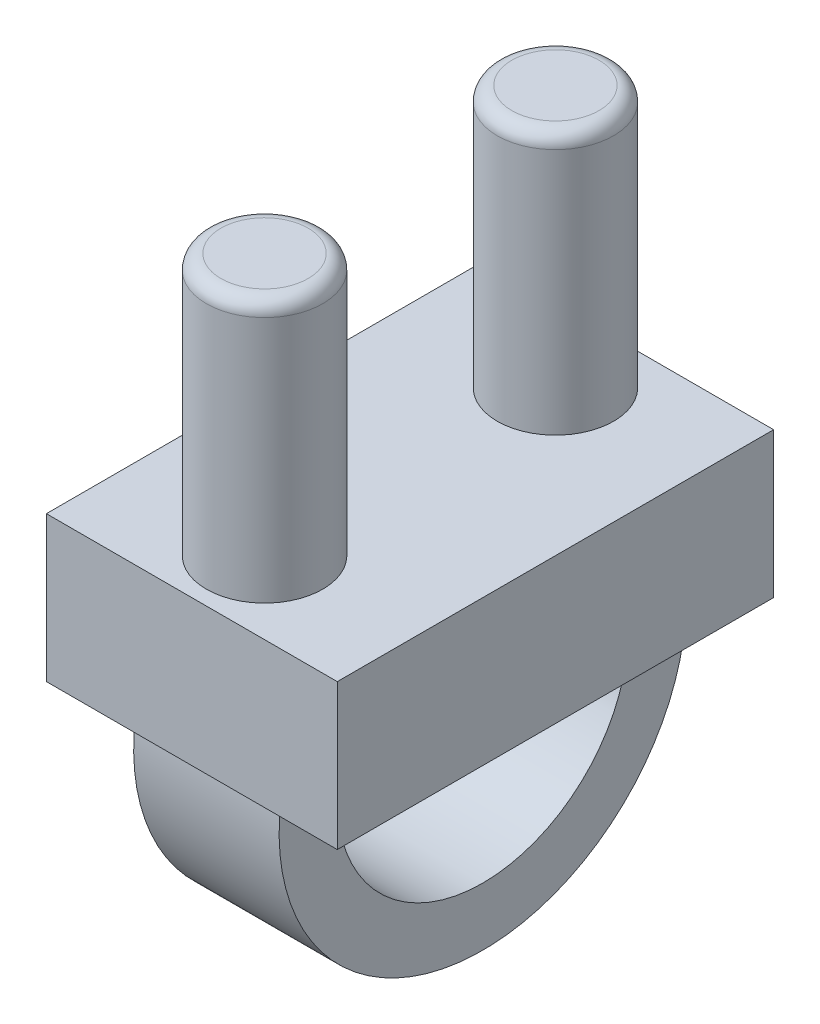
SolidWorks part; units mm, degrees
ref_plane "Front Plane" through (0, 0, 0) normal (0, 0, 1) x (1, 0, 0)
ref_plane "Top Plane" through (0, 0, 0) normal (0, 1, 0) x (1, 0, 0)
ref_plane "Right Plane" through (0, 0, 0) normal (1, 0, 0) x (0, 0, -1)
sketch "Sketch1" plane through (0, 0, 0) normal (0, 1, 0) x (1, 0, 0)
  line L1 (-1, 1.5) -> (1, 1.5)
  line L2 (-1, 1.5) -> (-1, -1.5)
  line L3 (-1, -1.5) -> (1, -1.5)
  line L4 (1, 1.5) -> (1, -1.5)
  line L5 (-1, 1.5) -> (1, -1.5) construction
  line L6 (-1, -1.5) -> (1, 1.5) construction
  point P0 (0, 0)
  dimension "D1" = 3
  dimension "D2" = 2
extrude "NP2 Implanter Lock Base" add sketch "Sketch1" along normal blind 1
sketch "Sketch2" plane through (0, 1, 0) normal (0, 1, 0) x (1, 0, 0)
  circle A1 centre (0, 1) radius 0.4
  circle A2 centre (0, -1) radius 0.4
  dimension "D1" = 0.8
  dimension "D4" = 0.8
  dimension "D2" = 0
  dimension "D3" = 1
  dimension "D5" = 0
  dimension "D6" = 1
extrude "Lock arms" add sketch "Sketch2" along normal blind 1.8
sketch "Sketch3" plane through (0, 0, 0) normal (1, 0, 0) x (0, 0, -1)
  line L3 (-1.5, 0) -> (1.5, 0) construction
  line L4 (-1.3856, 0) -> (-0.9798, 0)
  line L5 (0.9798, 0) -> (1.3856, 0)
  arc A2 (-0.9798, 0) -> (0.9798, 0) centre (0, -0.2) ccw
  arc A3 (-1.3856, 0) -> (1.3856, 0) centre (0, -0.2) ccw
  dimension "D3" = 1
  dimension "D4" = 0.4
  dimension "D1" = 0
  dimension "D2" = 0.2
extrude "Retreival Hooks" add sketch "Sketch3" along normal mid plane 1
fillet "Fillet1" radius 0.1 2 edges at (0, 2.8, 1.4) (0, 2.8, -0.6)
